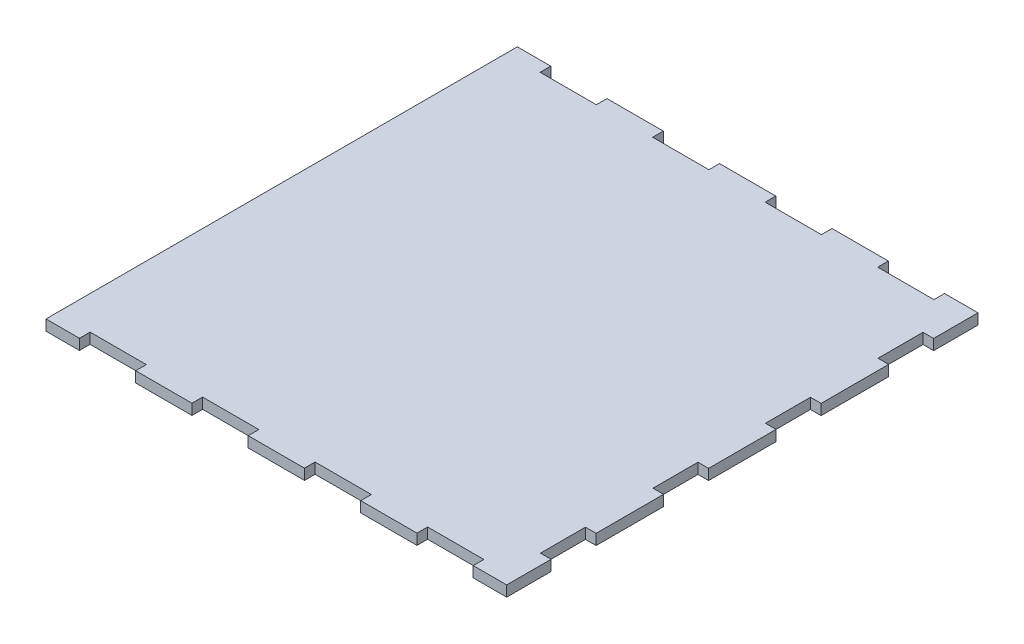
SolidWorks part; units mm, degrees
material "Balsa"
ref_plane "Front Plane" through (0, 0, 0) normal (0, 0, 1) x (1, 0, 0)
ref_plane "Top Plane" through (0, 0, 0) normal (0, 1, 0) x (1, 0, 0)
ref_plane "Right Plane" through (0, 0, 0) normal (1, 0, 0) x (0, 0, -1)
sketch "Sketch1" plane through (0, 0, 0) normal (0, 1, 0) x (1, 0, 0)
  line L0 (0, 133) -> (0, -133) construction
  line L1 (-130, -133) -> (130, -133)
  line L2 (-130, -133) -> (-130, 133)
  line L3 (-130, 133) -> (130, 133)
  line L4 (130, -133) -> (130, 133)
  point P4 (0, 133)
  point P6 (130, 0)
  dimension "D1" = 266
  dimension "D2" = 260
extrude "Boss-Extrude1" add sketch "Sketch1" along normal blind 6 contours L3 L4 L1 L2
sketch "Sketch2" plane through (0, 6, 0) normal (0, 1, 0) x (1, 0, 0)
  line L0 (-130, 0) -> (130, 0) construction
  line L1 (-130, -133) -> (-130, 133) construction
  line L2 (130, -133) -> (130, 133) construction
  line L3 (0, 133) -> (0, -133) construction
  line L4 (-130, 133) -> (130, 133) construction
  line L5 (-130, -133) -> (130, -133) construction
  line L6 (111.125, 133) -> (111.125, 127)
  line L7 (-15.875, 133) -> (-47.625, 133)
  line L8 (-15.875, 133) -> (-15.875, 127)
  line L9 (-15.875, 127) -> (-47.625, 127)
  line L10 (-47.625, 133) -> (-47.625, 127)
  line L11 (-79.375, 133) -> (-111.125, 133)
  line L12 (-79.375, 133) -> (-79.375, 127)
  line L13 (-79.375, 127) -> (-111.125, 127)
  line L14 (-111.125, 133) -> (-111.125, 127)
  line L15 (79.375, 127) -> (111.125, 127)
  line L16 (79.375, 133) -> (79.375, 127)
  line L17 (79.375, 133) -> (111.125, 133)
  line L18 (47.625, 133) -> (47.625, 127)
  line L19 (15.875, 127) -> (47.625, 127)
  line L20 (15.875, 133) -> (15.875, 127)
  line L21 (15.875, 133) -> (47.625, 133)
  line L22 (15.875, -133) -> (47.625, -133)
  line L23 (15.875, -133) -> (15.875, -127)
  line L24 (15.875, -127) -> (47.625, -127)
  line L25 (47.625, -133) -> (47.625, -127)
  line L26 (79.375, -133) -> (111.125, -133)
  line L27 (79.375, -133) -> (79.375, -127)
  line L28 (79.375, -127) -> (111.125, -127)
  line L29 (-111.125, -133) -> (-111.125, -127)
  line L30 (-79.375, -127) -> (-111.125, -127)
  line L31 (-79.375, -133) -> (-79.375, -127)
  line L32 (-79.375, -133) -> (-111.125, -133)
  line L33 (-47.625, -133) -> (-47.625, -127)
  line L34 (-15.875, -127) -> (-47.625, -127)
  line L35 (-15.875, -133) -> (-15.875, -127)
  line L36 (-15.875, -133) -> (-47.625, -133)
  line L37 (111.125, -133) -> (111.125, -127)
  line L38 (130, 133) -> (0, 0) construction
  line L39 (124, -82.55) -> (124, -107.95)
  line L40 (130, 19.05) -> (124, 19.05)
  line L41 (130, 19.05) -> (130, 44.45)
  line L42 (130, 44.45) -> (124, 44.45)
  line L43 (124, 19.05) -> (124, 44.45)
  line L44 (130, 82.55) -> (124, 82.55)
  line L45 (130, 82.55) -> (130, 107.95)
  line L46 (130, 107.95) -> (124, 107.95)
  line L47 (124, 82.55) -> (124, 107.95)
  line L48 (130, -107.95) -> (124, -107.95)
  line L49 (130, -82.55) -> (130, -107.95)
  line L50 (130, -82.55) -> (124, -82.55)
  line L51 (124, -19.05) -> (124, -44.45)
  line L52 (130, -44.45) -> (124, -44.45)
  line L53 (130, -19.05) -> (130, -44.45)
  line L54 (130, -19.05) -> (124, -19.05)
  point P12 (0, 0)
  point P22 (-31.75, 127)
  point P23 (-95.25, 127)
  point P59 (124, 31.75)
  point P60 (130, 31.75)
  point P61 (130, 95.25)
  dimension "D1" = 31.75
  dimension "D2" = 63.5
  dimension "D3" = 63.5
  dimension "D4" = 254
  dimension "D5" = 63.5
  dimension "D6" = 25.4
  dimension "D7" = 63.5
extrude "Tab Cut Outs" cut sketch "Sketch2" against normal up to surface (6 mm away) up to face at (0, 0, 0)
sketch "Sketch3" plane through (0, 6, 0) normal (0, 1, 0) x (1, 0, 0)
  line L104 (79.4766, -127.1016) -> (111.0234, -127.1016)
  line L105 (111.0234, -127.1016) -> (111.0234, -133.1016)
  line L106 (111.0234, -133.1016) -> (130.1016, -133.1016)
  line L107 (130.1016, -133.1016) -> (130.1016, -107.8484)
  line L108 (130.1016, -107.8484) -> (124.1016, -107.8484)
  line L109 (124.1016, -107.8484) -> (124.1016, -82.6516)
  line L110 (124.1016, -82.6516) -> (130.1016, -82.6516)
  line L111 (130.1016, -82.6516) -> (130.1016, -44.3484)
  line L112 (130.1016, -44.3484) -> (124.1016, -44.3484)
  line L113 (124.1016, -44.3484) -> (124.1016, -19.1516)
  line L114 (124.1016, -19.1516) -> (130.1016, -19.1516)
  line L115 (130.1016, -19.1516) -> (130.1016, 19.1516)
  line L116 (130.1016, 19.1516) -> (124.1016, 19.1516)
  line L117 (124.1016, 19.1516) -> (124.1016, 44.3484)
  line L118 (124.1016, 44.3484) -> (130.1016, 44.3484)
  line L119 (130.1016, 44.3484) -> (130.1016, 82.6516)
  line L120 (130.1016, 82.6516) -> (124.1016, 82.6516)
  line L121 (124.1016, 82.6516) -> (124.1016, 107.8484)
  line L122 (124.1016, 107.8484) -> (130.1016, 107.8484)
  line L123 (130.1016, 107.8484) -> (130.1016, 133.1016)
  line L124 (130.1016, 133.1016) -> (111.0234, 133.1016)
  line L125 (111.0234, 133.1016) -> (111.0234, 127.1016)
  line L126 (111.0234, 127.1016) -> (79.4766, 127.1016)
  line L127 (79.4766, 127.1016) -> (79.4766, 133.1016)
  line L128 (79.4766, 133.1016) -> (47.5234, 133.1016)
  line L129 (47.5234, 133.1016) -> (47.5234, 127.1016)
  line L130 (47.5234, 127.1016) -> (15.9766, 127.1016)
  line L131 (15.9766, 127.1016) -> (15.9766, 133.1016)
  line L132 (15.9766, 133.1016) -> (-15.9766, 133.1016)
  line L133 (-15.9766, 133.1016) -> (-15.9766, 127.1016)
  line L134 (-15.9766, 127.1016) -> (-47.5234, 127.1016)
  line L135 (-47.5234, 127.1016) -> (-47.5234, 133.1016)
  line L136 (-47.5234, 133.1016) -> (-79.4766, 133.1016)
  line L137 (-79.4766, 133.1016) -> (-79.4766, 127.1016)
  line L138 (-79.4766, 127.1016) -> (-111.0234, 127.1016)
  line L139 (-111.0234, 127.1016) -> (-111.0234, 133.1016)
  line L140 (-111.0234, 133.1016) -> (-130.1016, 133.1016)
  line L141 (-130.1016, 133.1016) -> (-130.1016, -133.1016)
  line L142 (-130.1016, -133.1016) -> (-111.0234, -133.1016)
  line L143 (-111.0234, -133.1016) -> (-111.0234, -127.1016)
  line L144 (-111.0234, -127.1016) -> (-79.4766, -127.1016)
  line L145 (-79.4766, -127.1016) -> (-79.4766, -133.1016)
  line L146 (-79.4766, -133.1016) -> (-47.5234, -133.1016)
  line L147 (-47.5234, -133.1016) -> (-47.5234, -127.1016)
  line L148 (-47.5234, -127.1016) -> (-15.9766, -127.1016)
  line L149 (-15.9766, -127.1016) -> (-15.9766, -133.1016)
  line L150 (-15.9766, -133.1016) -> (15.9766, -133.1016)
  line L151 (15.9766, -133.1016) -> (15.9766, -127.1016)
  line L152 (15.9766, -127.1016) -> (47.5234, -127.1016)
  line L153 (47.5234, -127.1016) -> (47.5234, -133.1016)
  line L154 (47.5234, -133.1016) -> (79.4766, -133.1016)
  line L155 (79.4766, -133.1016) -> (79.4766, -127.1016)
  line L156 (79.4766, -127.1016) -> (111.0234, -127.1016)
  line L157 (111.0234, -127.1016) -> (111.0234, -133.1016)
  line L158 (111.0234, -133.1016) -> (130.1016, -133.1016)
  line L159 (130.1016, -133.1016) -> (130.1016, -107.8484)
  line L160 (130.1016, -107.8484) -> (124.1016, -107.8484)
  line L161 (124.1016, -107.8484) -> (124.1016, -82.6516)
  line L162 (124.1016, -82.6516) -> (130.1016, -82.6516)
  line L163 (130.1016, -82.6516) -> (130.1016, -44.3484)
  line L164 (130.1016, -44.3484) -> (124.1016, -44.3484)
  line L165 (124.1016, -44.3484) -> (124.1016, -19.1516)
  line L166 (124.1016, -19.1516) -> (130.1016, -19.1516)
  line L167 (130.1016, -19.1516) -> (130.1016, 19.1516)
  line L168 (130.1016, 19.1516) -> (124.1016, 19.1516)
  line L169 (124.1016, 19.1516) -> (124.1016, 44.3484)
  line L170 (124.1016, 44.3484) -> (130.1016, 44.3484)
  line L171 (130.1016, 44.3484) -> (130.1016, 82.6516)
  line L172 (130.1016, 82.6516) -> (124.1016, 82.6516)
  line L173 (124.1016, 82.6516) -> (124.1016, 107.8484)
  line L174 (124.1016, 107.8484) -> (130.1016, 107.8484)
  line L175 (130.1016, 107.8484) -> (130.1016, 133.1016)
  line L176 (130.1016, 133.1016) -> (111.0234, 133.1016)
  line L177 (111.0234, 133.1016) -> (111.0234, 127.1016)
  line L178 (111.0234, 127.1016) -> (79.4766, 127.1016)
  line L179 (79.4766, 127.1016) -> (79.4766, 133.1016)
  line L180 (79.4766, 133.1016) -> (47.5234, 133.1016)
  line L181 (47.5234, 133.1016) -> (47.5234, 127.1016)
  line L182 (47.5234, 127.1016) -> (15.9766, 127.1016)
  line L183 (15.9766, 127.1016) -> (15.9766, 133.1016)
  line L184 (15.9766, 133.1016) -> (-15.9766, 133.1016)
  line L185 (-15.9766, 133.1016) -> (-15.9766, 127.1016)
  line L186 (-15.9766, 127.1016) -> (-47.5234, 127.1016)
  line L187 (-47.5234, 127.1016) -> (-47.5234, 133.1016)
  line L188 (-47.5234, 133.1016) -> (-79.4766, 133.1016)
  line L189 (-79.4766, 133.1016) -> (-79.4766, 127.1016)
  line L190 (-79.4766, 127.1016) -> (-111.0234, 127.1016)
  line L191 (-111.0234, 127.1016) -> (-111.0234, 133.1016)
  line L192 (-111.0234, 133.1016) -> (-130.1016, 133.1016)
  line L193 (-130.1016, 133.1016) -> (-130.1016, -133.1016)
  line L194 (-130.1016, -133.1016) -> (-111.0234, -133.1016)
  line L195 (-111.0234, -133.1016) -> (-111.0234, -127.1016)
  line L196 (-111.0234, -127.1016) -> (-79.4766, -127.1016)
  line L197 (-79.4766, -127.1016) -> (-79.4766, -133.1016)
  line L198 (-79.4766, -133.1016) -> (-47.5234, -133.1016)
  line L199 (-47.5234, -133.1016) -> (-47.5234, -127.1016)
  line L200 (-47.5234, -127.1016) -> (-15.9766, -127.1016)
  line L201 (-15.9766, -127.1016) -> (-15.9766, -133.1016)
  line L202 (-15.9766, -133.1016) -> (15.9766, -133.1016)
  line L203 (15.9766, -133.1016) -> (15.9766, -127.1016)
  line L204 (15.9766, -127.1016) -> (47.5234, -127.1016)
  line L205 (47.5234, -127.1016) -> (47.5234, -133.1016)
  line L206 (47.5234, -133.1016) -> (79.4766, -133.1016)
  line L207 (79.4766, -133.1016) -> (79.4766, -127.1016)
  dimension "D1" = 0.1016
extrude "KERF" [suppressed] add sketch "Sketch3" against normal up to surface (6 mm away)
